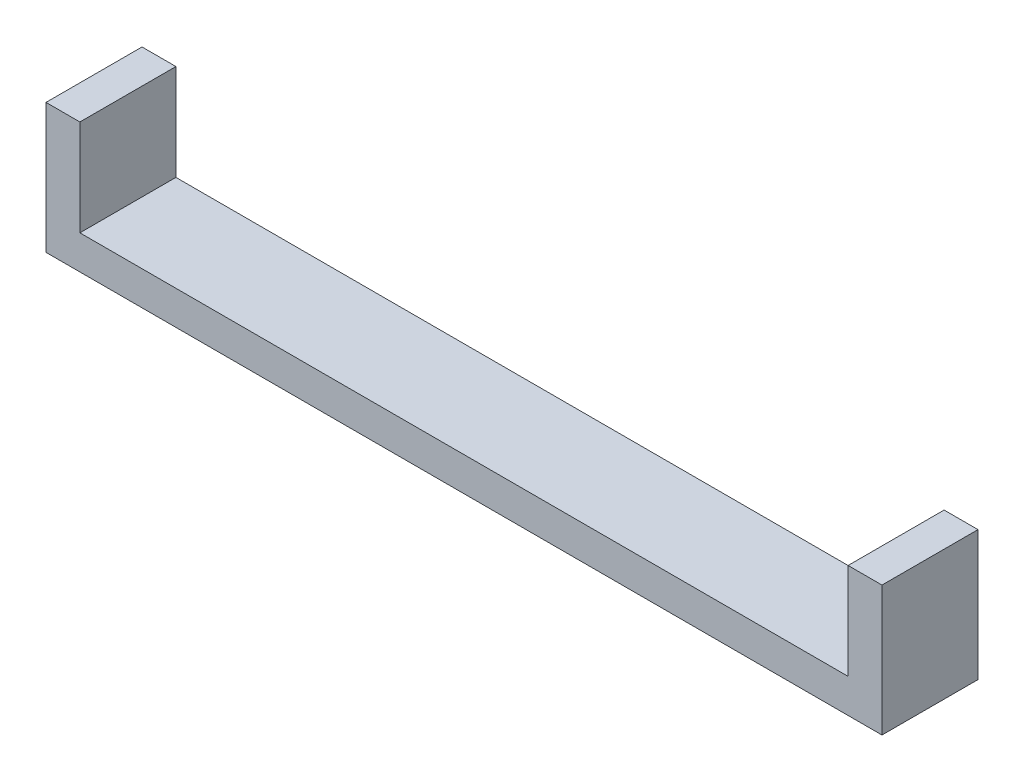
SolidWorks part; units mm, degrees
ref_plane "Front Plane" through (0, 0, 0) normal (0, 0, 1) x (1, 0, 0)
ref_plane "Top Plane" through (0, 0, 0) normal (0, 1, 0) x (1, 0, 0)
ref_plane "Right Plane" through (0, 0, 0) normal (1, 0, 0) x (0, 0, -1)
sketch "Sketch1" plane through (0, 0, 0) normal (1, 0, 0) x (0, 0, -1)
  line L0 (0, 0) -> (1.6017, 0) construction
  line L1 (1.5877, 2.75) -> (-1.5877, 2.75)
  line L2 (-1.5877, 2.75) -> (-3.1754, 0)
  line L3 (-3.1754, 0) -> (-1.5877, -2.75)
  line L4 (-1.5877, -2.75) -> (1.5877, -2.75)
  line L5 (1.5877, -2.75) -> (3.1754, 0)
  line L6 (3.1754, 0) -> (1.5877, 2.75)
  line L8 (-4.25, -4.25) -> (4.25, -4.25)
  line L9 (-4.25, -4.25) -> (-4.25, 4.25)
  line L10 (-4.25, 4.25) -> (4.25, 4.25)
  line L11 (4.25, -4.25) -> (4.25, 4.25)
  line L12 (-4.25, -4.25) -> (4.25, 4.25) construction
  line L13 (-4.25, 4.25) -> (4.25, -4.25) construction
  circle A0 centre (0, 0) radius 2.75 construction
  dimension "D1" = 5.5
  dimension "D2" = 8.5
  dimension "D3" = 8.5
extrude "Boss-Extrude1" add sketch "Sketch1" along normal blind 5
sketch "Sketch2" plane through (0, 0, 0) normal (-1, 0, 0) x (0, 0, 1)
  line L1 (-4.25, -4.25) -> (4.25, -4.25)
  line L2 (-4.25, -4.25) -> (-4.25, 4.25)
  line L3 (-4.25, 4.25) -> (4.25, 4.25)
  line L4 (4.25, -4.25) -> (4.25, 4.25)
  line L5 (-4.25, -4.25) -> (4.25, 4.25) construction
  line L6 (-4.25, 4.25) -> (4.25, -4.25) construction
  point P0 (0, 0)
extrude "Boss-Extrude2" add sketch "Sketch2" along normal blind 2
sketch "Sketch3" plane through (0, 0, 0) normal (1, 0, 0) x (0, 0, -1)
  circle A0 centre (0, 0) radius 1.5
  dimension "D1" = 3
extrude "Cut-Extrude1" cut sketch "Sketch3" against normal blind 2
sketch "Sketch4" plane through (0, -4.25, 0) normal (0, -1, 0) x (1, 0, 0)
  line L0 (5, -4.25) -> (-2, -4.25) construction
  line L1 (-2, 4.25) -> (80, 4.25)
  line L2 (-2, 4.25) -> (-2, -4.25)
  line L3 (-2, -4.25) -> (80, -4.25)
  line L4 (80, 4.25) -> (80, -4.25)
  dimension "D1" = 82
extrude "Boss-Extrude3" add sketch "Sketch4" along normal blind 3
sketch "Sketch5" plane through (0, -4.25, 0) normal (0, 1, 0) x (1, 0, 0)
  line L0 (80, -4.25) -> (5, -4.25) construction
  line L1 (80, 4.25) -> (73, 4.25)
  line L2 (80, 4.25) -> (80, -4.25)
  line L3 (80, -4.25) -> (73, -4.25)
  line L4 (73, 4.25) -> (73, -4.25)
  dimension "D1" = 7
extrude "Boss-Extrude4" add sketch "Sketch5" along normal up to surface (8.5 mm away) up to face at (1.5, 4.25, 0)
sketch "Sketch6" plane through (73, 0, 0) normal (-1, 0, 0) x (0, 0, 1)
  line L0 (-4.25, -4.25) -> (4.25, -4.25) construction
  line L1 (3.1754, 0) -> (1.5877, 2.75)
  line L2 (1.5877, 2.75) -> (-1.5877, 2.75)
  line L3 (-1.5877, 2.75) -> (-3.1754, 0)
  line L4 (-3.1754, 0) -> (-1.5877, -2.75)
  line L5 (-1.5877, -2.75) -> (1.5877, -2.75)
  line L6 (1.5877, -2.75) -> (3.1754, 0)
  circle A0 centre (0, 0) radius 2.75 construction
  dimension "D1" = 5.5
extrude "Cut-Extrude2" cut sketch "Sketch6" against normal blind 5
sketch "Sketch7" plane through (78, 0, 0) normal (-1, 0, 0) x (0, 0, 1)
  circle A0 centre (0, 0) radius 1.5
  dimension "D1" = 3
extrude "Cut-Extrude3" cut sketch "Sketch7" against normal blind 5
sketch "Sketch8" plane through (-2, 0, 0) normal (-1, 0, 0) x (0, 0, 1)
  line L0 (-1.5877, 2.75) -> (1.5877, 2.75) construction
  line L1 (1.5877, 2.75) -> (3.1754, 0) construction
  line L2 (3.1754, 0) -> (1.5877, -2.75) construction
  line L3 (1.5877, -2.75) -> (-1.5877, -2.75) construction
  line L4 (-1.5877, -2.75) -> (-3.1754, 0) construction
  line L5 (-3.1754, 0) -> (-1.5877, 2.75) construction
  line L6 (-1.5877, 2.75) -> (1.5877, 2.75)
  line L7 (1.5877, 2.75) -> (3.1754, 0)
  line L8 (3.1754, 0) -> (1.5877, -2.75)
  line L9 (1.5877, -2.75) -> (-1.5877, -2.75)
  line L10 (-1.5877, -2.75) -> (-3.1754, 0)
  line L11 (-3.1754, 0) -> (-1.5877, 2.75)
extrude "Cut-Extrude4" cut sketch "Sketch8" against normal blind 10
sketch "Sketch9" plane through (5, 0, 0) normal (1, 0, 0) x (0, 0, -1)
  line L1 (-4.25, 4.25) -> (4.25, 4.25)
  line L2 (-4.25, 4.25) -> (-4.25, -4.25)
  line L3 (-4.25, -4.25) -> (4.25, -4.25)
  line L4 (4.25, 4.25) -> (4.25, -4.25)
  circle A0 centre (0, 0) radius 1.5
  dimension "D1" = 3
extrude "Boss-Extrude5" add sketch "Sketch9" against normal blind 2
sketch "Sketch10" plane through (80, 0, 0) normal (1, 0, 0) x (0, 0, -1)
  line L0 (-3.1754, 0) -> (-1.5877, 2.75) construction
  line L1 (-1.5877, -2.75) -> (-3.1754, 0) construction
  line L2 (1.5877, -2.75) -> (-1.5877, -2.75) construction
  line L3 (3.1754, 0) -> (1.5877, -2.75) construction
  line L4 (1.5877, 2.75) -> (3.1754, 0) construction
  line L5 (-1.5877, 2.75) -> (1.5877, 2.75) construction
  line L6 (-3.1754, 0) -> (-1.5877, 2.75)
  line L7 (-1.5877, -2.75) -> (-3.1754, 0)
  line L8 (1.5877, -2.75) -> (-1.5877, -2.75)
  line L9 (3.1754, 0) -> (1.5877, -2.75)
  line L10 (1.5877, 2.75) -> (3.1754, 0)
  line L11 (-1.5877, 2.75) -> (1.5877, 2.75)
extrude "Cut-Extrude5" cut sketch "Sketch10" against normal blind 2
sketch "Sketch11" plane through (73, 0, 0) normal (-1, 0, 0) x (0, 0, 1)
  line L1 (-4.25, 4.25) -> (4.25, 4.25)
  line L2 (-4.25, 4.25) -> (-4.25, -4.25)
  line L3 (-4.25, -4.25) -> (4.25, -4.25)
  line L4 (4.25, 4.25) -> (4.25, -4.25)
  circle A0 centre (0, 0) radius 1.5
  dimension "D1" = 3
extrude "Boss-Extrude6" add sketch "Sketch11" against normal blind 2
sketch "Sketch12" plane through (3, 0, 0) normal (-1, 0, 0) x (0, 0, 1)
  line L0 (-3.1754, 0) -> (-1.5877, 2.75) construction
  line L1 (-1.5877, -2.75) -> (-3.1754, 0) construction
  line L2 (-1.5877, -2.75) -> (1.5877, -2.75) construction
  line L3 (1.5877, -2.75) -> (3.1754, 0) construction
  line L4 (3.1754, 0) -> (1.5877, 2.75) construction
  line L5 (-1.5877, 2.75) -> (1.5877, 2.75) construction
  line L6 (-3.1754, 0) -> (-1.5877, 2.75)
  line L7 (-1.5877, -2.75) -> (-3.1754, 0)
  line L8 (-1.5877, -2.75) -> (1.5877, -2.75)
  line L9 (1.5877, -2.75) -> (3.1754, 0)
  line L10 (3.1754, 0) -> (1.5877, 2.75)
  line L11 (-1.5877, 2.75) -> (1.5877, 2.75)
extrude "Boss-Extrude7" add sketch "Sketch12" along normal up to surface (5 mm away)
sketch "Sketch13" plane through (75, 0, 0) normal (1, 0, 0) x (0, 0, -1)
  line L0 (-1.5877, 2.75) -> (-3.1754, 0) construction
  line L1 (-3.1754, 0) -> (-1.5877, -2.75) construction
  line L2 (-1.5877, -2.75) -> (1.5877, -2.75) construction
  line L3 (1.5877, -2.75) -> (3.1754, 0) construction
  line L4 (3.1754, 0) -> (1.5877, 2.75) construction
  line L5 (1.5877, 2.75) -> (-1.5877, 2.75) construction
  line L6 (-1.5877, 2.75) -> (-3.1754, 0)
  line L7 (-3.1754, 0) -> (-1.5877, -2.75)
  line L8 (-1.5877, -2.75) -> (1.5877, -2.75)
  line L9 (1.5877, -2.75) -> (3.1754, 0)
  line L10 (3.1754, 0) -> (1.5877, 2.75)
  line L11 (1.5877, 2.75) -> (-1.5877, 2.75)
extrude "Boss-Extrude8" add sketch "Sketch13" along normal up to surface (5 mm away) up to face at (80, 0, 0)
sketch "Sketch14" plane through (-2, 0, 0) normal (-1, 0, 0) x (0, 0, 1)
  line L1 (-4.25, 4.25) -> (4.25, 4.25)
  line L2 (-4.25, 4.25) -> (-4.25, -7.25)
  line L3 (-4.25, -7.25) -> (4.25, -7.25)
  line L4 (4.25, 4.25) -> (4.25, -7.25)
extrude "Cut-Extrude6" cut sketch "Sketch14" against normal blind 4
sketch "Sketch15" plane through (80, 0, 0) normal (1, 0, 0) x (0, 0, -1)
  line L1 (-4.25, 4.25) -> (4.25, 4.25)
  line L2 (-4.25, 4.25) -> (-4.25, -7.25)
  line L3 (-4.25, -7.25) -> (4.25, -7.25)
  line L4 (4.25, 4.25) -> (4.25, -7.25)
extrude "Cut-Extrude7" cut sketch "Sketch15" against normal blind 4
sketch "Sketch16" plane through (5, 0, 0) normal (1, 0, 0) x (0, 0, -1)
  circle A0 centre (0, 0) radius 1.5
extrude "Cut-Extrude8" cut sketch "Sketch16" against normal blind 4
sketch "Sketch17" plane through (75, 0, 0) normal (-1, 0, 0) x (0, 0, 1)
  circle A0 centre (0, 0) radius 1.5
extrude "Cut-Extrude9" cut sketch "Sketch17" against normal blind 4
sketch "Sketch19" plane through (5, 0, 0) normal (1, 0, 0) x (0, 0, -1)
  line L1 (-4.25, 4.25) -> (4.25, 4.25)
  line L2 (-4.25, 4.25) -> (-4.25, -4.25)
  line L3 (-4.25, -4.25) -> (4.25, -4.25)
  line L4 (4.25, 4.25) -> (4.25, -4.25)
extrude "Boss-Extrude9" add sketch "Sketch19" against normal up to surface (3 mm away) up to face at (2, 0, 1.5)
sketch "Sketch20" plane through (73, 0, 0) normal (-1, 0, 0) x (0, 0, 1)
  line L1 (-4.25, 4.25) -> (4.25, 4.25)
  line L2 (-4.25, 4.25) -> (-4.25, -4.25)
  line L3 (-4.25, -4.25) -> (4.25, -4.25)
  line L4 (4.25, 4.25) -> (4.25, -4.25)
extrude "Boss-Extrude10" add sketch "Sketch20" against normal up to surface (3 mm away) up to face at (76, 0, -1.5)
